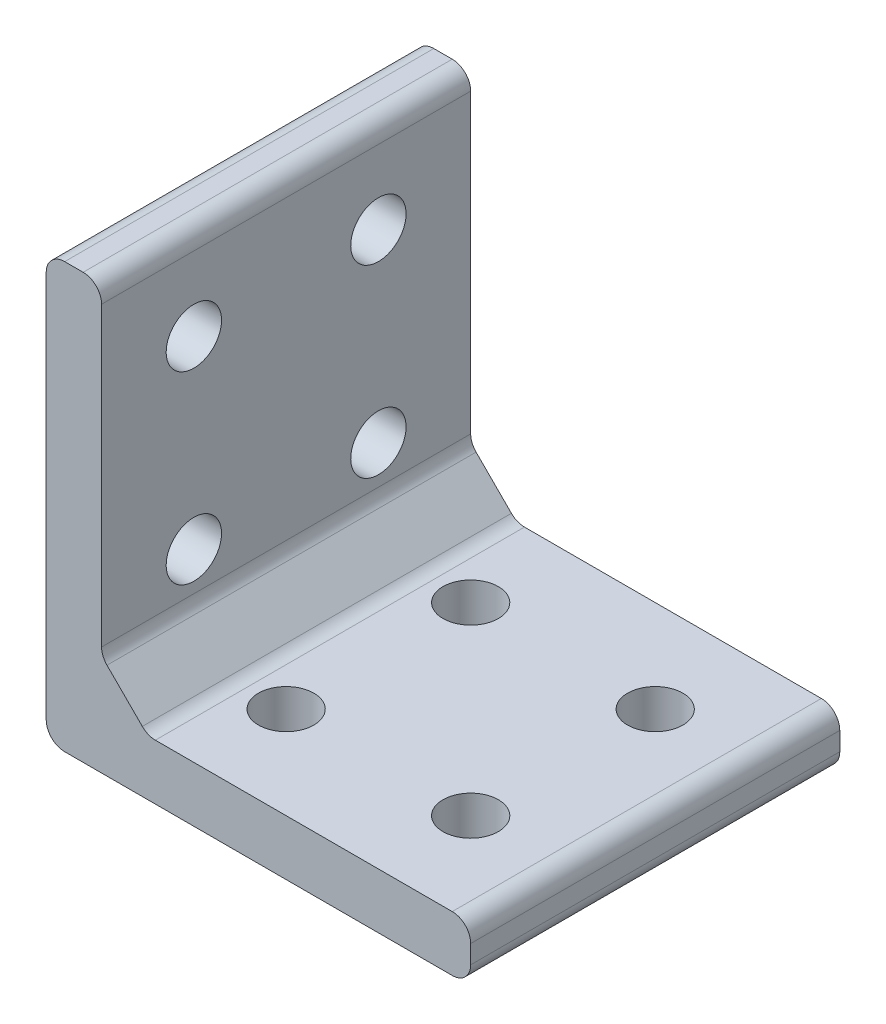
SolidWorks part; units mm, degrees
ref_plane "Plan de face" through (0, 0, 0) normal (0, 0, 1) x (1, 0, 0)
ref_plane "Plan de dessus" through (0, 0, 0) normal (0, 1, 0) x (1, 0, 0)
ref_plane "Plan de droite" through (0, 0, 0) normal (1, 0, 0) x (0, 0, -1)
sketch "Esquisse1" plane through (0, 0, 0) normal (0, 0, 1) x (1, 0, 0)
  line L0 (23, 0) -> (0, 0)
  line L1 (0, 0) -> (0, 23)
  line L2 (0, 23) -> (3, 23)
  line L3 (3, 23) -> (3, 3)
  line L4 (3, 3) -> (23, 3)
  line L5 (23, 3) -> (23, 0)
  dimension "D1" = 3
  dimension "D2" = 3
  dimension "D3" = 20
  dimension "D4" = 20
extrude "Boss.-Extru.1" add sketch "Esquisse1" along normal blind 20
sketch "Esquisse2" plane through (0, 3, 0) normal (0, 1, 0) x (1, 0, 0)
  line L2 (3, -20) -> (3, 0) construction
  line L3 (23, -20) -> (3, -20) construction
  circle A16 centre (8, -15) radius 1.5
  circle A17 centre (18, -15) radius 1.5
  circle A18 centre (18, -5) radius 1.5
  circle A19 centre (8, -5) radius 1.5
  dimension "D1" = 3
  dimension "D2" = 2
  dimension "D4" = 5
  dimension "D5" = 5
  dimension "D3" = 2
extrude "Enlèv. mat.-Extru.1" cut sketch "Esquisse2" against normal blind 20
sketch "Esquisse3" plane through (3, 0, 0) normal (1, 0, 0) x (0, 0, -1)
  line L2 (-20, 23) -> (0, 23) construction
  line L3 (-20, 3) -> (-20, 23) construction
  circle A16 centre (-15, 18) radius 1.5
  circle A17 centre (-5, 18) radius 1.5
  circle A18 centre (-5, 8) radius 1.5
  circle A19 centre (-15, 8) radius 1.5
  dimension "D1" = 3
  dimension "D2" = 5
  dimension "D3" = 5
extrude "Enlèv. mat.-Extru.2" cut sketch "Esquisse3" against normal blind 20
chamfer "Chanfrein1" distance 2.5 angle 45 1 edges at (3, 3, 10)
fillet "Congé2" radius 1 7 edges at (23, 3, 10) (23, 0, 10) (3, 23, 10) (0, 23, 10) (0, 0, 10) (3, 5.5, 10) (5.5, 3, 10)
